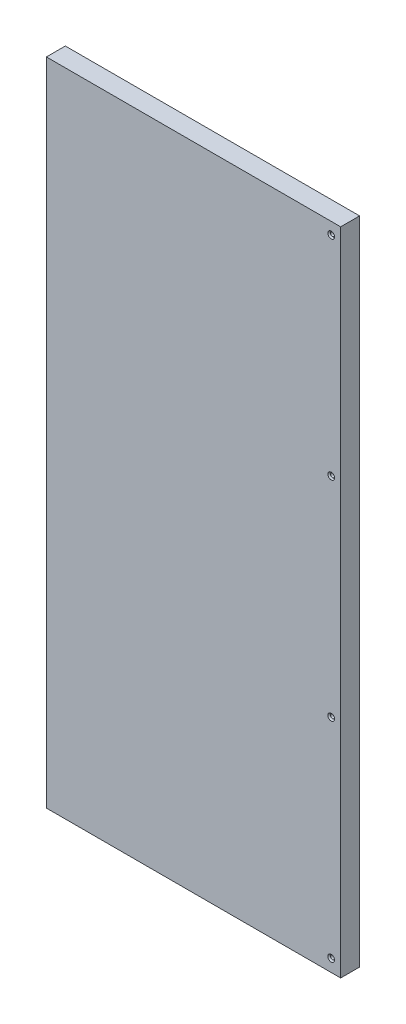
SolidWorks part; units mm, degrees
ref_plane "Front Plane" through (0, 0, 0) normal (0, 0, 1) x (1, 0, 0)
ref_plane "Top Plane" through (0, 0, 0) normal (0, 1, 0) x (1, 0, 0)
ref_plane "Right Plane" through (0, 0, 0) normal (1, 0, 0) x (0, 0, -1)
sketch "Sketch1" plane through (0, 0, 0) normal (0, 0, 1) x (1, 0, 0)
  line L1 (-124.39, 275) -> (124.39, 275)
  line L2 (-124.39, 275) -> (-124.39, -275)
  line L3 (-124.39, -275) -> (124.39, -275)
  line L4 (124.39, 275) -> (124.39, -275)
  point P4 (124.39, 0)
  point P5 (0, -275)
  dimension "D1" = 550
  dimension "D2" = 248.78
extrude "Boss-Extrude1" add sketch "Sketch1" along normal blind 16 contours L2 L3 L4 L1
hole_wizard "CSK for #4 Flat Head Machine Screw (100)1" positions "Sketch2" profile "Sketch3" countersink size "#4" standard "ANSI Inch" end condition up to next
sketch "Sketch2" plane through (0, 0, 16) normal (0, 0, 1) x (1, 0, 0)
  line L0 (124.39, 275) -> (124.39, -275) construction
  line L1 (-124.39, -275) -> (124.39, -275) construction
  point P0 (116.39, -264.5)
  dimension "D1" = 8
  dimension "D2" = 10.5
sketch "Sketch3" plane through (116.39, -264.5, 16) normal (1, 0, 0) x (0, -1, 0)
  line L0 (0, 0) -> (0, 16)
  line L1 (0, 16) -> (1.6319, 16)
  line L2 (1.6319, 16) -> (1.6319, 1.0284)
  line L3 (1.6319, 1.0284) -> (2.8575, 0)
  line L5 (2.8575, 0) -> (0, 0)
  line L6 (-1.6319, 1.0284) -> (-2.8575, 0) construction
  line L11 (0, -6.35) -> (0, 107.95) construction
  dimension "Thru Hole Dia." = 3.2639
  dimension "Thru Hole Depth" = 16
  dimension "Near C'Sink Dia." = 5.715
  dimension "Near C'Sink Angle" = 100
pattern_linear "LPattern1" count 4 spacing 176.5 along (0, 1, 0) of "CSK for #4 Flat Head Machine Screw (100)1"
equation "\"Length\"= 45cm"
equation "\"Width\"= 16cm"
equation "\"Curvature radius\"= 13mm"
equation "\"Extra\"= 5cm"
equation "\"D1@Sketch1\"=\"Length\"+\"Extra\"*2"
